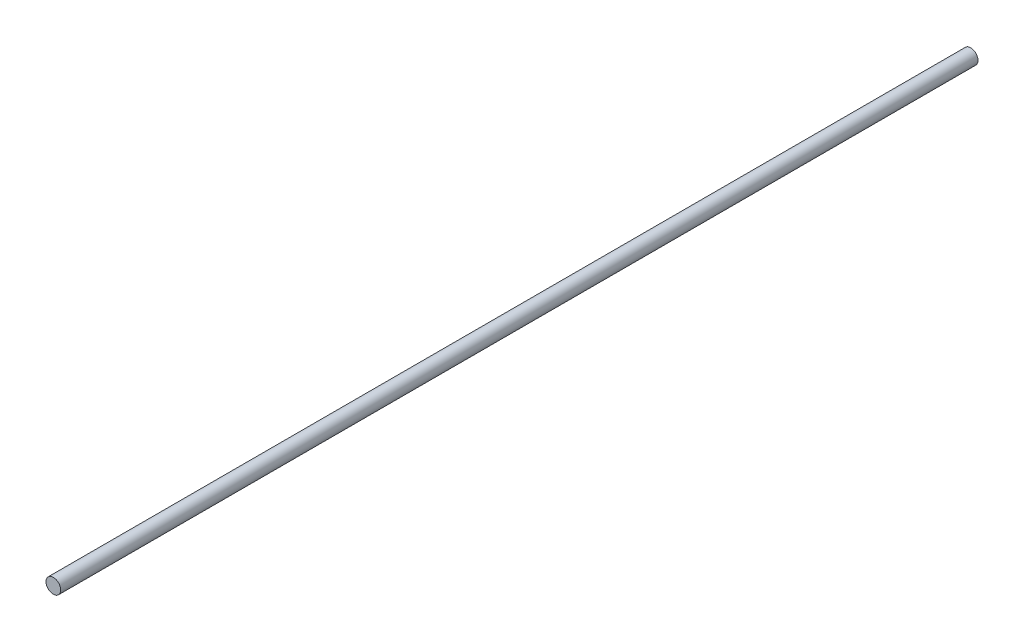
SolidWorks part; units mm, degrees
ref_plane "Front Plane" through (0, 0, 0) normal (0, 0, 1) x (1, 0, 0)
ref_plane "Top Plane" through (0, 0, 0) normal (0, 1, 0) x (1, 0, 0)
ref_plane "Right Plane" through (0, 0, 0) normal (1, 0, 0) x (0, 0, -1)
sketch "Sketch1" plane through (0, 0, 0) normal (0, 0, 1) x (1, 0, 0)
  circle A0 centre (0, 0) radius 4
  dimension "D1" = 8
extrude "Boss-Extrude1" add sketch "Sketch1" against normal blind 500
sketch "Sketch2" plane through (0, 0, 0) normal (0, 0, 1) x (1, 0, 0)
  circle A0 centre (0, 0) radius 4
  dimension "D1" = 8
curve "Helix/Spiral1" pitch 2 height 400 turns 200
sketch "Croquis1" plane through (0, 0, -500) normal (0, 0, -1) x (-1, 0, 0)
  line L1 (3, 6.4049) -> (5, 6.4049)
  line L2 (3, 6.4049) -> (3, -5.5951)
  line L3 (3, -5.5951) -> (5, -5.5951)
  line L4 (5, 6.4049) -> (5, -5.5951)
  dimension "D1" = 12
  dimension "D2" = 2
  dimension "D3" = 3
extrude "Cortar-Extruir1" cut sketch "Croquis1" against normal blind 10
